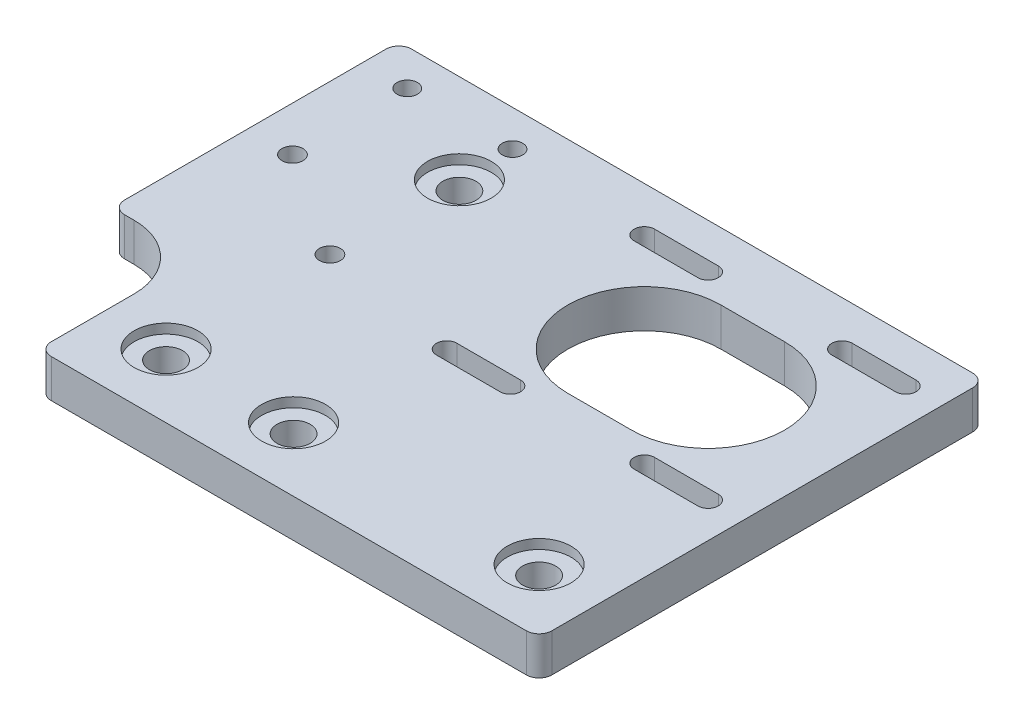
SolidWorks part; units mm, degrees
material "6061 Alloy"
ref_plane "Front" through (0, 0, 0) normal (0, 0, 1) x (1, 0, 0)
ref_plane "Top" through (0, 0, 0) normal (0, 1, 0) x (1, 0, 0)
ref_plane "Right" through (0, 0, 0) normal (1, 0, 0) x (0, 0, -1)
sketch "Sketch3" plane through (0, 0, 0) normal (0, 1, 0) x (1, 0, 0)
  line L0 (20, 70) -> (20, 20) construction
  line L1 (0, 0) -> (78.5, 0)
  line L2 (0, 0) -> (0, 70) construction
  line L3 (0, 70) -> (78.5, 70)
  line L4 (78.5, 0) -> (78.5, 70)
  line L5 (20, 20) -> (78.5, 20) construction
  line L6 (10, 70) -> (10, 10) construction
  line L7 (10, 10) -> (78.5, 10) construction
  line L8 (0, 70) -> (-13.5, 70)
  line L11 (-13.5, 70) -> (-13.5, 25)
  line L12 (-13.5, 25) -> (0, 25)
  line L14 (47.5, 47.5) -> (57.5, 47.5) construction
  line L15 (47.5, 59.5) -> (57.5, 59.5)
  line L16 (47.5, 35.5) -> (57.5, 35.5)
  line L17 (32, 63) -> (42, 63) construction
  line L18 (37, 32) -> (68, 32) construction
  line L19 (37, 32) -> (37, 63) construction
  line L20 (37, 63) -> (68, 63) construction
  line L21 (68, 32) -> (68, 63) construction
  line L22 (37, 32) -> (68, 63) construction
  line L23 (37, 63) -> (68, 32) construction
  line L24 (32, 64.6) -> (42, 64.6)
  line L25 (32, 61.4) -> (42, 61.4)
  line L26 (63, 63) -> (73, 63) construction
  line L27 (63, 64.6) -> (73, 64.6)
  line L28 (63, 61.4) -> (73, 61.4)
  line L29 (63, 32) -> (73, 32) construction
  line L30 (63, 33.6) -> (73, 33.6)
  line L31 (63, 30.4) -> (73, 30.4)
  line L32 (32, 32) -> (42, 32) construction
  line L33 (32, 33.6) -> (42, 33.6)
  line L34 (32, 30.4) -> (42, 30.4)
  line L35 (24.9094, 47.5) -> (47.5, 47.5) construction
  line L36 (73, 63) -> (78.5, 63) construction
  line L37 (32, 63) -> (20, 63) construction
  line L38 (-6.5, 64.325) -> (-6.5, 46.325) construction
  line L39 (10, 35.7) -> (10, 64.325) construction
  line L40 (10, 64.325) -> (-6.5, 64.325) construction
  line L44 (0, 25) -> (0, 0)
  circle A0 centre (10, 56) radius 2.6
  circle A1 centre (10, 10) radius 2.6
  circle A2 centre (68.5, 10) radius 2.6
  arc A3 (47.5, 59.5) -> (47.5, 35.5) centre (47.5, 47.5) ccw
  arc A4 (57.5, 35.5) -> (57.5, 59.5) centre (57.5, 47.5) ccw
  arc A5 (32, 64.6) -> (32, 61.4) centre (32, 63) ccw
  arc A6 (42, 61.4) -> (42, 64.6) centre (42, 63) ccw
  arc A7 (63, 64.6) -> (63, 61.4) centre (63, 63) ccw
  arc A8 (73, 61.4) -> (73, 64.6) centre (73, 63) ccw
  arc A9 (63, 33.6) -> (63, 30.4) centre (63, 32) ccw
  arc A10 (73, 30.4) -> (73, 33.6) centre (73, 32) ccw
  arc A11 (32, 33.6) -> (32, 30.4) centre (32, 32) ccw
  arc A12 (42, 30.4) -> (42, 33.6) centre (42, 32) ccw
  circle A13 centre (10, 35.7) radius 2.7 construction
  circle A14 centre (-6.5, 46.325) radius 2.7 construction
  circle A15 centre (10, 10) radius 4.5 construction
  circle A16 centre (10, 64.325) radius 1.6 construction
  circle A17 centre (-6.5, 64.325) radius 1.6 construction
  circle A18 centre (30, 10) radius 2.6
  point P21 (52.5, 47.5)
  point P26 (52.5, 47.5)
  point P33 (37, 63)
  point P39 (68, 63)
  point P46 (68, 32)
  point P53 (37, 32)
  dimension "D7" = 5.2
  dimension "D10" = 12
  dimension "D12" = 1.6
  dimension "D15" = 10
  dimension "D17" = 18
  dimension "D18" = 7
  dimension "D20" = 2.35
  dimension "D21" = 5.4
  dimension "D22" = 9
  dimension "D23" = 3.2
  dimension "D25" = 5.5
  dimension "D26" = 20
  dimension "D16" = 10.625
  dimension "D8" = 14
  dimension "D9" = 10.7
  dimension "D1" = 70
  dimension "D2" = 10
  dimension "D3" = 20
  dimension "D4" = 20
  dimension "D5" = 10
  dimension "D6" = 10
  dimension "D11" = 31
  dimension "D13" = 10
  dimension "D14" = 12
  dimension "D19" = 16.5
  dimension "D24" = 22.5
extrude "Boss-Extrude1" add sketch "Sketch3" along normal blind 6
sketch "Sketch5" plane through (0, 6, 0) normal (0, 1, 0) x (1, 0, 0)
  circle A0 centre (10, 56) radius 5
  circle A1 centre (10, 10) radius 5
  circle A2 centre (30, 10) radius 5
  circle A3 centre (68.5, 10) radius 5
  dimension "D1" = 10
fillet "Fillet1" radius 10 1 edges at (0, 3, -25)
sketch "Sketch7" plane through (0, 6, 0) normal (0, 1, 0) x (1, 0, 0)
  line L0 (-6.5, 64.325) -> (10, 64.325) construction
  line L1 (-6.5, 67.325) -> (10, 67.325) construction
  line L2 (-6.5, 61.325) -> (10, 61.325) construction
  arc A0 (-6.5, 67.325) -> (-6.5, 61.325) centre (-6.5, 64.325) ccw construction
  arc A1 (10, 61.325) -> (10, 67.325) centre (10, 64.325) ccw construction
  circle A2 centre (-6.5, 64.325) radius 1.35
  circle A3 centre (10, 64.325) radius 1.35
  point P2 (1.75, 64.325)
  dimension "D1" = 3
  dimension "D2" = 2.7
hole_wizard "M3 Clearance Hole1" positions "Sketch8" profile "Sketch9" hole size "M3" standard "ANSI Metric" end condition through all
sketch "Sketch8" plane through (0, 6, 0) normal (0, 1, 0) x (1, 0, 0)
  point P0 (10, 64.325)
  point P3 (-6.5, 64.325)
sketch "Sketch9" plane through (10, 6, -64.325) normal (1, 0, 0) x (0, 0, 1)
  line L0 (0, 0) -> (0, 6)
  line L1 (0, 6) -> (1.6, 6)
  line L2 (1.6, 6) -> (1.6, 0)
  line L5 (1.6, 0) -> (0, 0)
  line L11 (0, -6.35) -> (0, 107.95) construction
  dimension "Thru Hole Dia." = 3.2
  dimension "Thru Hole Depth" = 6
hole_wizard "M4x0.7 Tapped Hole1" positions "Sketch10" profile "Sketch11" tap size "M4x0.7" standard "ANSI Metric" end condition through all
sketch "Sketch10" plane through (0, 6, 0) normal (0, 1, 0) x (1, 0, 0)
  circle A0 centre (15.65, 30.05) radius 11.5
  point P0 (-6.5, 46.325)
  point P3 (10, 35.7)
  dimension "D3" = 23
  dimension "D1" = 5.65
  dimension "D2" = 5.65
sketch "Sketch11" plane through (-6.5, 6, -46.325) normal (1, 0, 0) x (0, 0, 1)
  line L0 (0, 0) -> (0, 6)
  line L1 (0, 6) -> (1.65, 6)
  line L2 (1.65, 6) -> (1.65, 0)
  line L5 (1.65, 0) -> (0, 0)
  line L11 (0, -6.35) -> (0, 107.95) construction
  dimension "Thru Tap Drill Dia." = 3.3
  dimension "Thru Tap Drill Depth" = 6
cosmetic thread "Hole Thread1" parameters "D2"=4
cosmetic thread "Hole Thread2" parameters "D2"=4
fillet "Fillet2" radius 2 5 edges at (-13.5, 3, -25) (0, 3, 0) (-13.5, 3, -70) (78.5, 3, 0) (78.5, 3, -70)
sketch "Sketch12" plane through (0, 6, 0) normal (0, 1, 0) x (1, 0, 0)
  circle A4 centre (10, 35.7) radius 2.65
  circle A5 centre (-6.5, 46.325) radius 2.65
  circle A6 centre (-6.5, 46.325) radius 5
  circle A7 centre (10, 35.7) radius 5
  dimension "D1" = 10
  dimension "D2" = 5.3
extrude "Counterbore" cut sketch "Sketch5" against normal blind 1.5
mirror "Mirror1" [suppressed]
delete or keep bodies "Body-Delete/Keep 1" [suppressed] type delete bodies bodies 118
